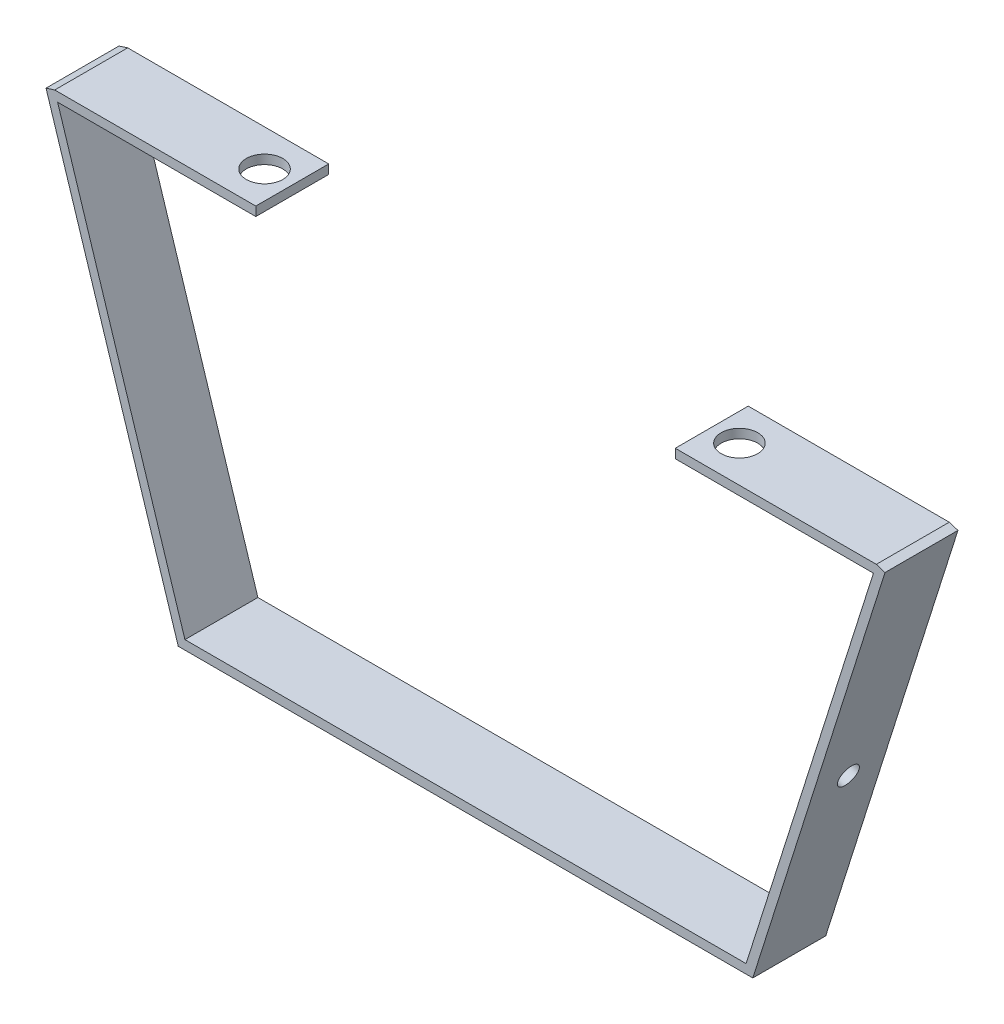
SolidWorks part; units mm, degrees
ref_plane "Front Plane" through (0, 0, 0) normal (0, 0, 1) x (1, 0, 0)
ref_plane "Top Plane" through (0, 0, 0) normal (0, 1, 0) x (1, 0, 0)
ref_plane "Right Plane" through (0, 0, 0) normal (1, 0, 0) x (0, 0, -1)
sketch "Sketch1" plane through (0, 0, 0) normal (0, 0, 1) x (1, 0, 0)
  line L0 (-95.9147, -24.4509) -> (104.1103, -24.4509)
  line L1 (104.1103, -24.4509) -> (150.1478, 120.8292)
  line L2 (-95.9147, -24.4509) -> (-141.9522, 120.8292)
  line L3 (101.7858, -21.2759) -> (147.1211, 121.7883)
  line L4 (-93.5902, -21.2759) -> (101.7858, -21.2759)
  line L5 (-93.5902, -21.2759) -> (-138.9256, 121.7883)
  line L6 (-141.9522, 120.8292) -> (-138.9256, 121.7883)
  line L7 (147.1211, 121.7883) -> (150.1478, 120.8292)
  dimension "D1" = 152.4
  dimension "D2" = 152.4
  dimension "D3" = 200.025
  dimension "D4" = 292.1
  dimension "D5" = 3.175
extrude "Boss-Extrude1" add sketch "Sketch1" along normal blind 25.4
sketch "Sketch4" plane through (0, 0, 0) normal (0, 0, -1) x (-1, 0, 0)
  line L0 (-147.1211, 121.7883) -> (138.9256, 121.7883)
  line L2 (-146.115, 118.6133) -> (137.9194, 118.6133)
  line L4 (-147.1211, 121.7883) -> (-101.7858, -21.2759) construction
  line L6 (141.9522, 120.8292) -> (138.9256, 121.7883)
  line L7 (-147.1211, 121.7883) -> (-150.1478, 120.8292)
  line L8 (93.5902, -21.2759) -> (138.9256, 121.7883) construction
  line L9 (-146.115, 118.6133) -> (-150.1478, 120.8292)
  line L10 (137.9194, 118.6133) -> (141.9522, 120.8292)
  line L12 (-77.1211, 121.7883) -> (68.9256, 121.7883)
  line L13 (-77.1211, 121.7883) -> (-77.1211, 118.6133)
  line L14 (-77.1211, 118.6133) -> (68.9256, 118.6133)
  line L15 (68.9256, 121.7883) -> (68.9256, 118.6133)
  line M6 (138.9256, 121.7883) -> (93.5902, -21.2759)
  line M8 (-101.7858, -21.2759) -> (-147.1211, 121.7883)
  dimension "D1" = 3.175
  dimension "D2" = 70
  dimension "D3" = 70
extrude "Boss-Extrude2" add sketch "Sketch4" against normal blind 25.4 contours L13 L0 L2 M8 | L0 L15 L2 M6
sketch "Sketch6" plane through (0, 121.7883, 0) normal (0, 1, 0) x (1, 0, 0)
  line L1 (-138.9256, -25.4) -> (-138.9256, 0) construction
  line L2 (147.1211, -25.4) -> (147.1211, 0) construction
  line L3 (147.1211, 0) -> (77.1211, 0) construction
  circle A0 centre (-78.5756, -12.7) radius 6.35
  circle A1 centre (86.7711, -12.7) radius 6.35
  dimension "D1" = 12.7
  dimension "D2" = 12.7
  dimension "D3" = 60.35
  dimension "D4" = 60.35
extrude "Cut-Extrude1" cut sketch "Sketch6" against normal blind 10
sketch "Sketch7" plane through (101.6509, -32.2119, 0) normal (0.9533, -0.3021, 0) x (0, 0, -1)
  line L0 (0, 8.1414) -> (0, 160.5414) construction
  circle A0 centre (-12.7, 76.2859) radius 3.675
  dimension "D2" = 7.35
  dimension "D1" = 12.7
extrude "Cut-Extrude2" cut sketch "Sketch7" against normal blind 3.175
